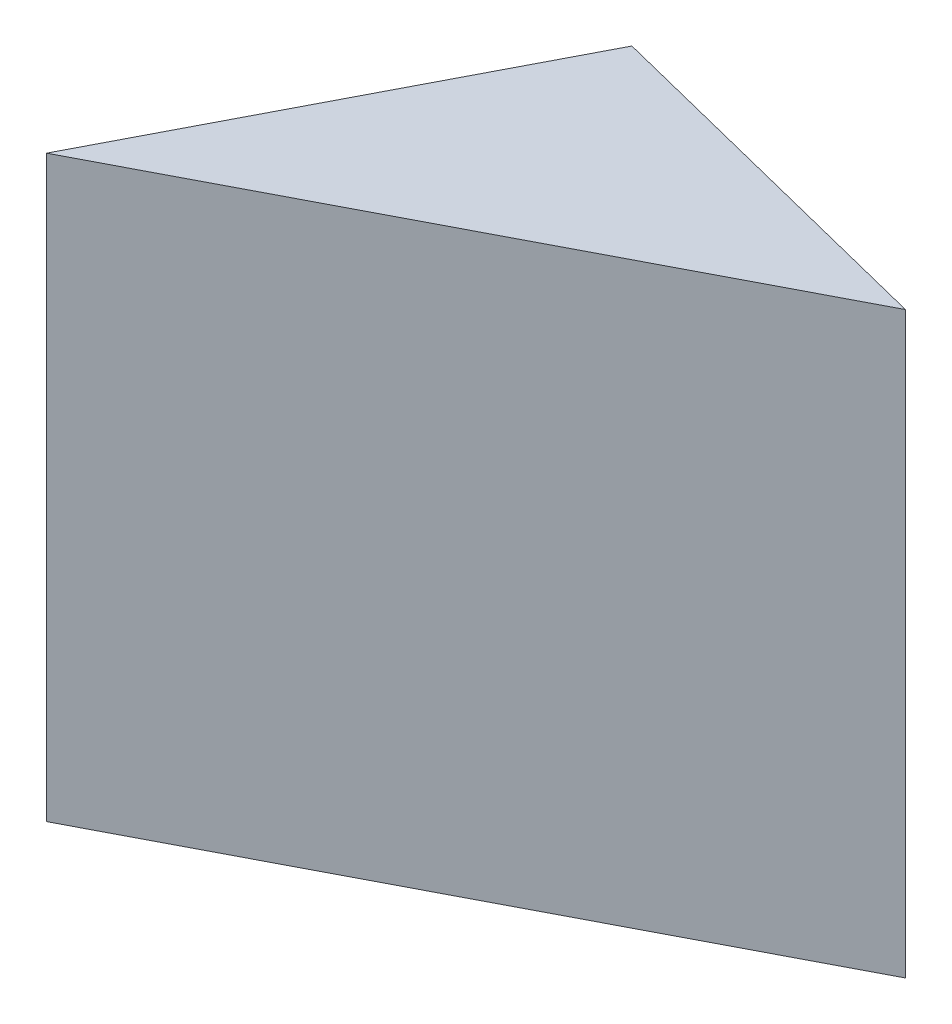
SolidWorks part; units mm, degrees
ref_plane "Front" through (0, 0, 0) normal (0, 0, 1) x (1, 0, 0)
ref_plane "Top" through (0, 0, 0) normal (0, 1, 0) x (1, 0, 0)
ref_plane "Right" through (0, 0, 0) normal (1, 0, 0) x (0, 0, -1)
sketch "Sketch1" plane through (0, 0, 0) normal (0, 1, 0) x (1, 0, 0)
  line L0 (0, 0) -> (6.9046, 13.3164)
  line L1 (6.9046, 13.3164) -> (19.5149, 10.1572)
  line L2 (19.5149, 10.1572) -> (0, 0)
  dimension "D1" = 15
  dimension "D2" = 13
  dimension "D3" = 22
extrude "Extrude1" add sketch "Sketch1" along normal blind 20
